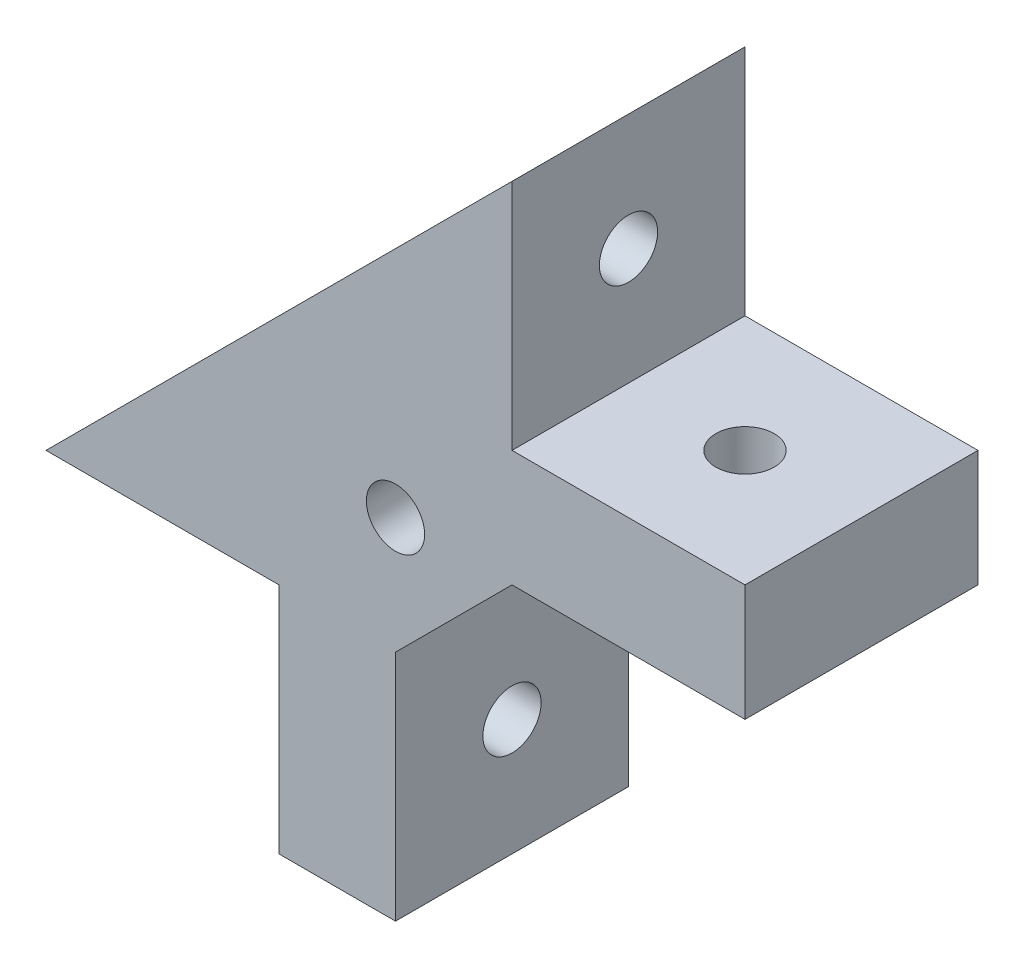
SolidWorks part; units mm, degrees
ref_plane "Front Plane" through (0, 0, 0) normal (0, 0, 1) x (1, 0, 0)
ref_plane "Top Plane" through (0, 0, 0) normal (0, 1, 0) x (1, 0, 0)
ref_plane "Right Plane" through (0, 0, 0) normal (1, 0, 0) x (0, 0, -1)
sketch "Sketch1" plane through (0, 0, 0) normal (0, 0, 1) x (1, 0, 0)
  line L0 (0, 0) -> (20, 20)
  line L1 (20, 20) -> (20, 10)
  line L2 (10, 0) -> (10, -10)
  line L3 (10, -10) -> (15, -10)
  line L4 (20, 10) -> (30, 10)
  line L5 (15, -10) -> (15, 0)
  line L6 (0, 0) -> (10, 0)
  line L7 (15, 0) -> (20, 5)
  line L8 (20, 5) -> (30, 5)
  line L9 (30, 10) -> (30, 5)
  circle A0 centre (15, 5) radius 1.25
  point P4 (0, 0)
  point P11 (0, 0)
  dimension "D6" = 2.5
  dimension "D1" = 45
  dimension "D2" = 10
  dimension "D3" = 5
  dimension "D4" = 10
  dimension "D5" = 28.2843
extrude "Main" add sketch "Sketch1" along normal blind 10
sketch "Sketch2" plane through (20, 0, 0) normal (1, 0, 0) x (0, 0, -1)
  line L0 (0, 0) -> (-10, -10) construction
  line L1 (-10, 0) -> (0, -10) construction
  line L2 (-10, 10) -> (0, 20) construction
  line L3 (-10, 20) -> (0, 10) construction
  circle A0 centre (-5, -5) radius 1.25
  circle A1 centre (-5, 15) radius 1.25
  point P20 (-5, 15)
  dimension "D1" = 2.5
extrude "Cut-Extrude1" cut sketch "Sketch2" against normal through all
sketch "Sketch3" plane through (0, 0, 0) normal (0, -1, 0) x (-1, 0, 0)
  line L0 (0, 0) -> (-10, -10) construction
  line L1 (0, -10) -> (-10, 0) construction
  line L2 (-10, -10) -> (-10, 0) construction
  line L3 (-10, 0) -> (-15, 0) construction
  line L4 (-20, 0) -> (-30, -10) construction
  line L5 (-20, -10) -> (-30, 0) construction
  circle A0 centre (-5, -5) radius 1.25
  circle A1 centre (-25, -5) radius 1.25
  point P23 (-25, -5)
  dimension "D1" = 2.5
extrude "Cut-Extrude2" cut sketch "Sketch3" against normal through all
